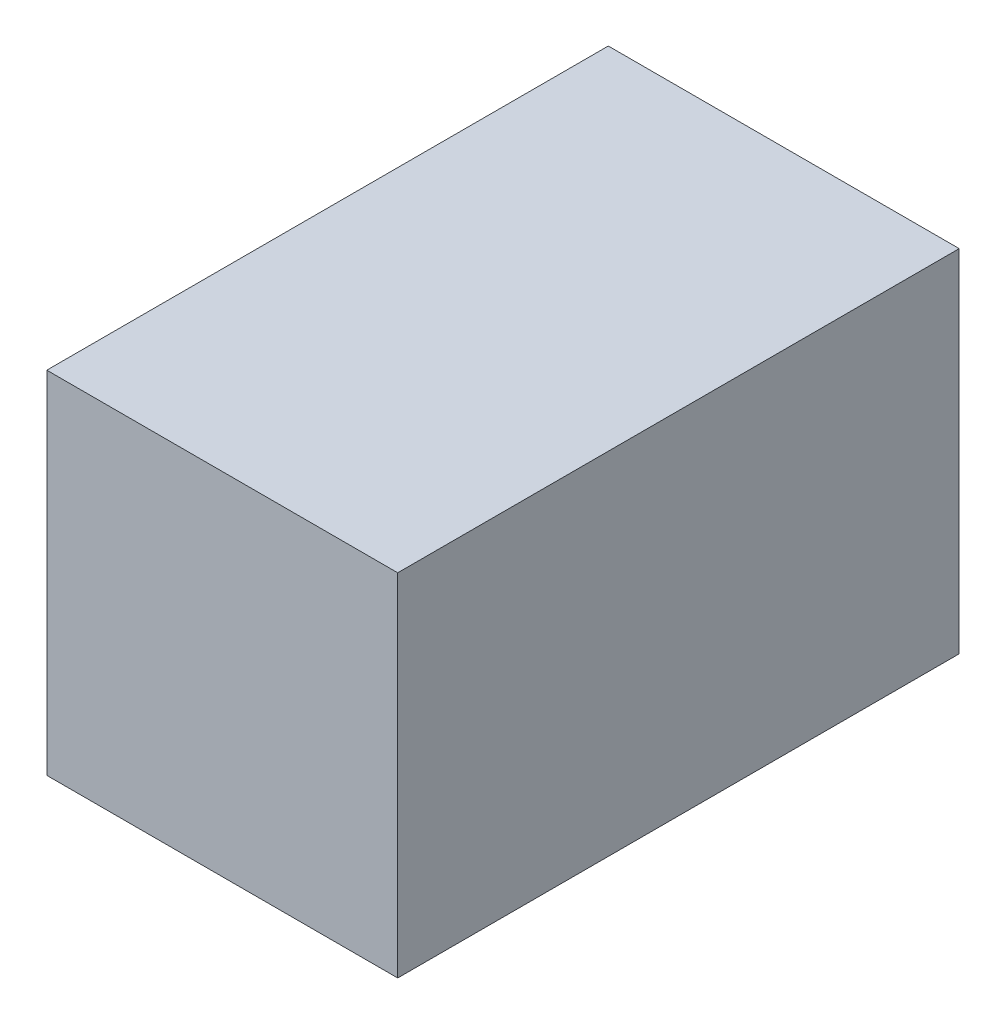
SolidWorks part; units mm, degrees
material "Polyurethane Foam Rigid"
ref_plane "Front Plane" through (0, 0, 0) normal (0, 0, 1) x (1, 0, 0)
ref_plane "Top Plane" through (0, 0, 0) normal (0, 1, 0) x (1, 0, 0)
ref_plane "Right Plane" through (0, 0, 0) normal (1, 0, 0) x (0, 0, -1)
sketch "Sketch1" plane through (0, 0, 0) normal (0, 1, 0) x (1, 0, 0)
  line L1 (-31.75, 50.8) -> (31.75, 50.8)
  line L2 (-31.75, 50.8) -> (-31.75, -50.8)
  line L3 (-31.75, -50.8) -> (31.75, -50.8)
  line L4 (31.75, 50.8) -> (31.75, -50.8)
  line L5 (-31.75, 50.8) -> (31.75, -50.8) construction
  line L6 (-31.75, -50.8) -> (31.75, 50.8) construction
  point P0 (0, 0)
  dimension "D1" = 101.6
  dimension "D2" = 63.5
extrude "Boss-Extrude1" add sketch "Sketch1" along normal blind 63.5
